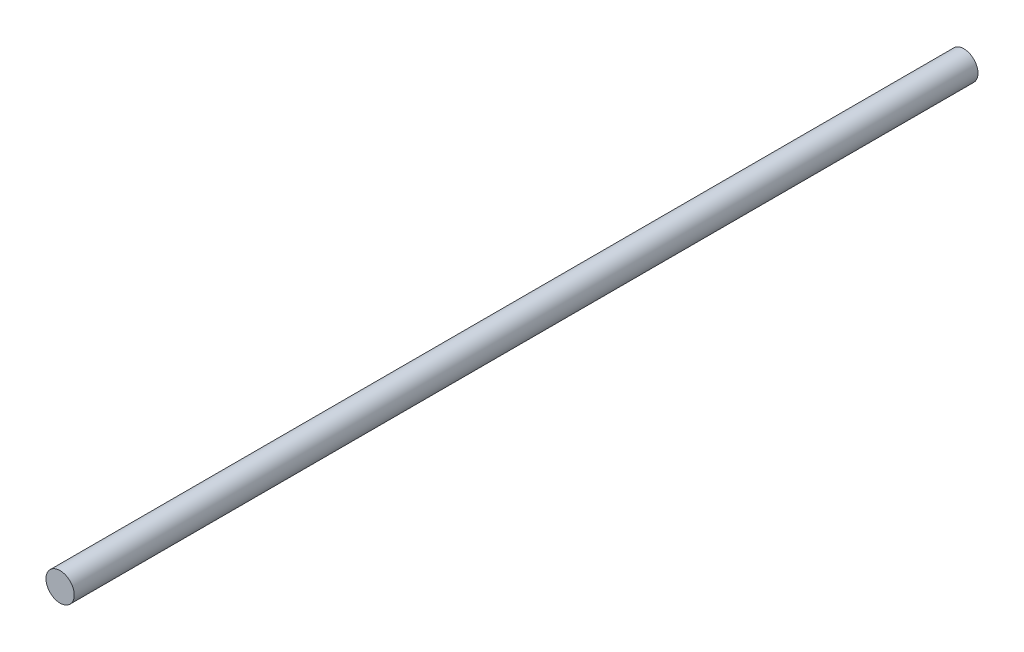
SolidWorks part; units mm, degrees
material "AISI 1020"
ref_plane "Front Plane" through (0, 0, 0) normal (0, 0, 1) x (1, 0, 0)
ref_plane "Top Plane" through (0, 0, 0) normal (0, 1, 0) x (1, 0, 0)
ref_plane "Right Plane" through (0, 0, 0) normal (1, 0, 0) x (0, 0, -1)
sketch "Sketch2" plane through (0, 0, 0) normal (0, 0, 1) x (1, 0, 0)
  circle A0 centre (0, 0) radius 4.7625
  dimension "D1" = 9.525
extrude "Boss-Extrude1" add sketch "Sketch2" along normal blind 304.8
